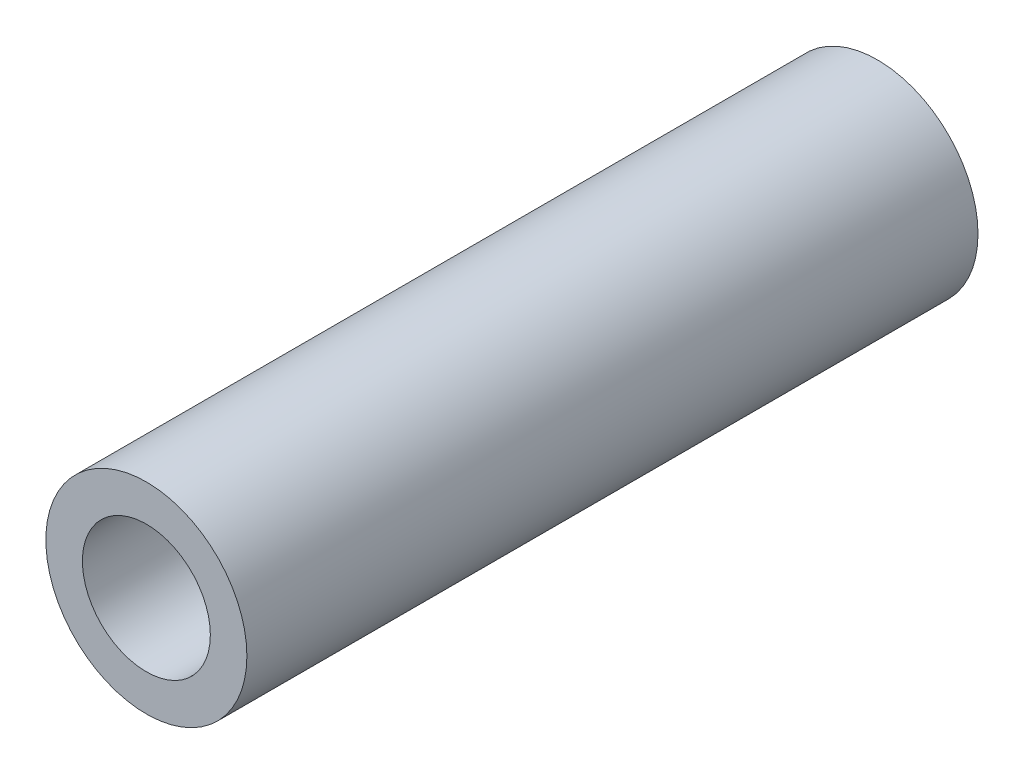
SolidWorks part; units mm, degrees
ref_plane "Płaszczyzna przednia" through (0, 0, 0) normal (0, 0, 1) x (1, 0, 0)
ref_plane "Płaszczyzna górna" through (0, 0, 0) normal (0, 1, 0) x (1, 0, 0)
ref_plane "Płaszczyzna prawa" through (0, 0, 0) normal (1, 0, 0) x (0, 0, -1)
sketch "Sketch1" plane through (0, 0, 0) normal (0, 0, 1) x (1, 0, 0)
  circle A0 centre (0, 0) radius 1.75
  circle A1 centre (0, 0) radius 2.75
  dimension "D1" = 3.5
  dimension "D2" = 5.5
extrude "Boss-Extrude1" add sketch "Sketch1" along normal blind 20
